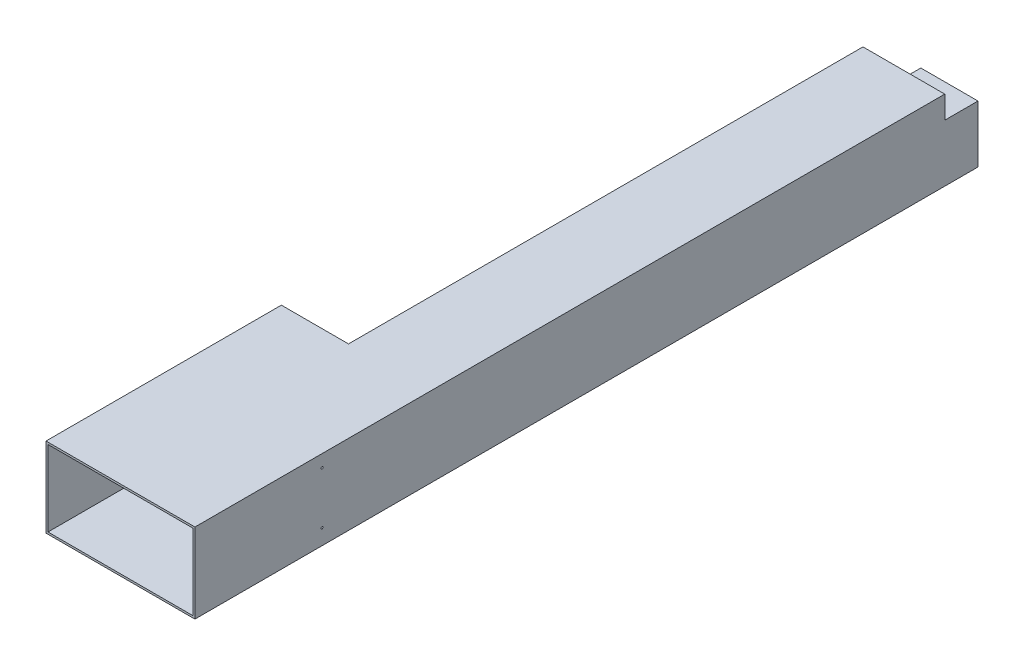
SolidWorks part; units mm, degrees
other "DetailItem1"
other "DetailItem2"
other "DetailItem3"
ref_plane "Front Plane" through (0, 0, 0) normal (0, 0, 1) x (1, 0, 0)
ref_plane "Top Plane" through (0, 0, 0) normal (0, 1, 0) x (1, 0, 0)
ref_plane "Right Plane" through (0, 0, 0) normal (1, 0, 0) x (0, 0, -1)
sketch "Sketch1" plane through (0, 0, 0) normal (0, 0, 1) x (1, 0, 0)
  line L0 (11050, 5850) -> (-150, 5850)
  line L1 (-150, 5850) -> (-150, -150)
  line L2 (-150, -150) -> (11050, -150)
  line L3 (11050, -150) -> (11050, 5850)
  line L4 (0, 5700) -> (0, 0)
  line L5 (0, 0) -> (10900, 0)
  line L6 (10900, 0) -> (10900, 5700)
  line L7 (10900, 5700) -> (0, 5700)
  line L8 (0, 5700) -> (0, 0)
  line L9 (0, 0) -> (10900, 0)
  line L10 (10900, 0) -> (10900, 5700)
  line L11 (10900, 5700) -> (0, 5700)
  dimension "D1" = 0
  dimension "D2" = 150
extrude "Extrude1" add sketch "Sketch1" against normal offset from surface (17700 mm away) 150
sketch "Sketch2" plane through (0, 0, -56240) normal (0, 0, -1) x (-1, 0, 0)
  line L0 (-11050, -150) -> (-4900, -150)
  line L1 (-4900, -150) -> (-4900, 5850)
  line L2 (-4900, 5850) -> (-11050, 5850)
  line L3 (-11050, 5850) -> (-11050, -150)
  line L4 (-10900, 5700) -> (-10900, 0)
  line L5 (-10900, 0) -> (-5050, 0)
  line L6 (-5050, 0) -> (-5050, 5700)
  line L7 (-5050, 5700) -> (-10900, 5700)
  line L8 (-10900, 5700) -> (-10900, 0)
  line L9 (-10900, 0) -> (-5050, 0)
  line L10 (-5050, 0) -> (-5050, 5700)
  line L11 (-5050, 5700) -> (-10900, 5700)
  dimension "D1" = 0
  dimension "D2" = 150
extrude "Extrude2" add sketch "Sketch2" against normal up to surface (38540 mm away) up to face at (5450, 2850, -17700)
sketch "Sketch3" plane through (0, 0, -58740) normal (0, 0, -1) x (-1, 0, 0)
  line L0 (-11050, -150) -> (-6750, -150)
  line L1 (-6750, -150) -> (-6750, 4150)
  line L2 (-6750, 4150) -> (-11050, 4150)
  line L3 (-11050, 4150) -> (-11050, -150)
  line L4 (-10900, 4000) -> (-10900, 0)
  line L5 (-10900, 0) -> (-6900, 0)
  line L6 (-6900, 0) -> (-6900, 4000)
  line L7 (-6900, 4000) -> (-10900, 4000)
  line L8 (-10900, 4000) -> (-10900, 0)
  line L9 (-10900, 0) -> (-6900, 0)
  line L10 (-6900, 0) -> (-6900, 4000)
  line L11 (-6900, 4000) -> (-10900, 4000)
  dimension "D1" = 0
  dimension "D2" = 150
extrude "Extrude3" add sketch "Sketch3" against normal up to surface (2500 mm away) up to face at (7975, 2850, -56240)
sketch "Sketch4" plane through (0, 0, -58740) normal (0, 0, -1) x (-1, 0, 0)
  line L4 (-11050, 4150) -> (-11050, -150)
  line L5 (-11050, -150) -> (-6750, -150)
  line L6 (-6750, -150) -> (-6750, 4150)
  line L7 (-6750, 4150) -> (-11050, 4150)
  line L8 (-11050, 4150) -> (-11050, -150)
  line L9 (-11050, -150) -> (-6750, -150)
  line L10 (-6750, -150) -> (-6750, 4150)
  line L11 (-6750, 4150) -> (-11050, 4150)
  dimension "D1" = 0
extrude "Extrude4" add sketch "Sketch4" along normal blind 150
sketch "Sketch5" plane through (0, 0, -56240) normal (0, 0, -1) x (-1, 0, 0)
  line L10 (-11050, 5850) -> (-11050, 4150)
  line L11 (-11050, 4150) -> (-10900, 4150)
  line L12 (-10900, 4150) -> (-10900, 5700)
  line L13 (-10900, 5700) -> (-5050, 5700)
  line L14 (-5050, 5700) -> (-5050, 0)
  line L15 (-5050, 0) -> (-6750, 0)
  line L16 (-6750, 0) -> (-6750, -150)
  line L17 (-6750, -150) -> (-4900, -150)
  line L18 (-4900, -150) -> (-4900, 5850)
  line L19 (-4900, 5850) -> (-11050, 5850)
  line L20 (-11050, 5850) -> (-11050, 4150)
  line L21 (-11050, 4150) -> (-6750, 4150)
  line L26 (-6750, 4150) -> (-6750, -150)
  line L27 (-6750, -150) -> (-4900, -150)
  line L28 (-4900, -150) -> (-4900, 5850)
  line L29 (-4900, 5850) -> (-11050, 5850)
  dimension "D1" = 0
extrude "Extrude5" add sketch "Sketch5" along normal blind 150
sketch "Sketch6" plane through (0, 0, -17700) normal (0, 0, -1) x (-1, 0, 0)
  line L0 (-4900, 5850) -> (-11050, 5850) construction
  line L1 (-4900, -150) -> (-4900, 5850) construction
  line L8 (150, 5850) -> (-4900, 5850)
  line L9 (-4900, 5850) -> (-4900, 5700)
  line L10 (-4900, 5700) -> (0, 5700)
  line L11 (0, 5700) -> (0, 0)
  line L12 (0, 0) -> (-4900, 0)
  line L13 (-4900, 0) -> (-4900, -150)
  line L14 (-4900, -150) -> (150, -150)
  line L15 (150, -150) -> (150, 5850)
  line L16 (150, 5850) -> (-5050, 5850)
  line L21 (-5050, 5850) -> (-5050, -150)
  line L22 (-5050, -150) -> (150, -150)
  line L23 (150, -150) -> (150, 5850)
  dimension "D2" = 150
  dimension "D1" = 0
extrude "Extrude7" add sketch "Sketch6" against normal blind 150
sketch "Sketch7" plane through (11050, 0, 0) normal (1, 0, 0) x (0, 0, -1)
  line L0 (0, -150) -> (0, 5850) construction
  line L1 (56390, 5850) -> (0, 5850) construction
  line L2 (58890, -150) -> (0, -150) construction
  circle A0 centre (9560, 4920) radius 75
  circle A1 centre (9560, 1020) radius 75
  dimension "D1" = 150
  dimension "D2" = 150
  dimension "D3" = 9560
  dimension "D4" = 9560
  dimension "D5" = 930
  dimension "D6" = 1170
extrude "Cut-Extrude1" cut sketch "Sketch7" against normal up to next
sketch "Sketch8" plane through (0, -150, 0) normal (0, -1, 0) x (1, 0, 0)
  line L0 (-150, 0) -> (11050, 0) construction
  line L1 (11050, -58890) -> (11050, 0) construction
  circle A0 centre (8050, -22960) radius 50
  dimension "D3" = 100
  dimension "D1" = 22960
  dimension "D2" = 3000
extrude "Cut-Extrude2" cut sketch "Sketch8" against normal up to next
